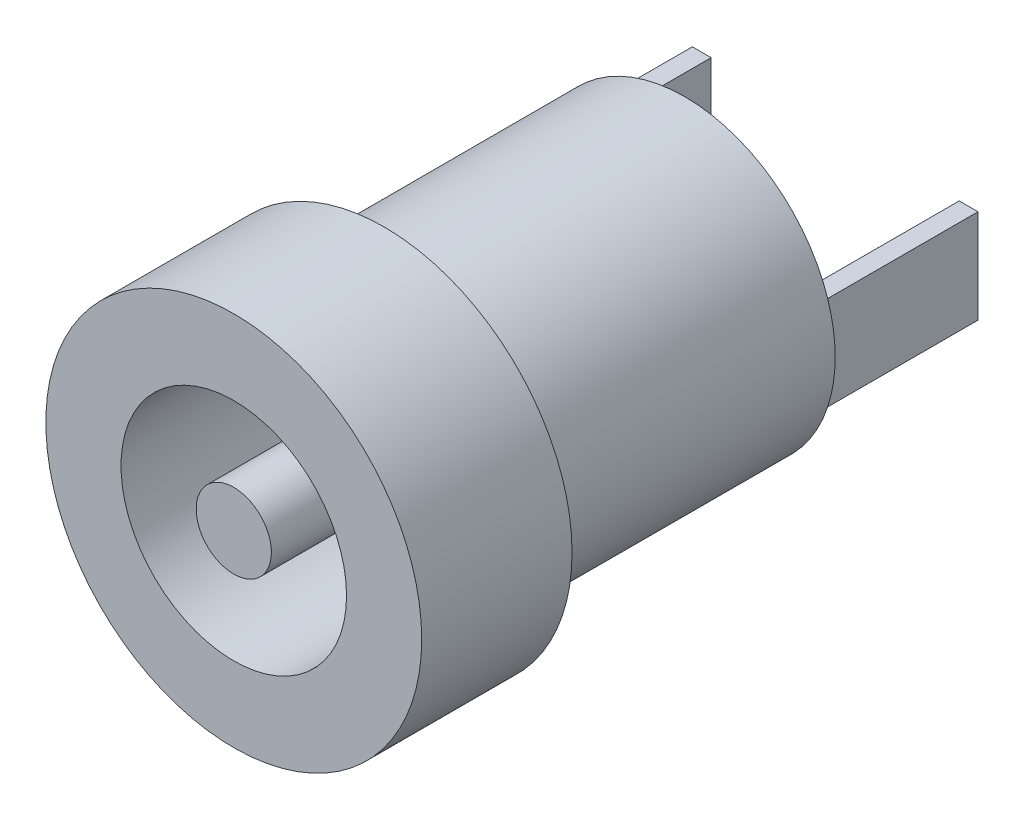
SolidWorks part; units mm, degrees
ref_plane "Front Plane" through (0, 0, 0) normal (0, 0, 1) x (1, 0, 0)
ref_plane "Top Plane" through (0, 0, 0) normal (0, 1, 0) x (1, 0, 0)
ref_plane "Right Plane" through (0, 0, 0) normal (1, 0, 0) x (0, 0, -1)
sketch "Sketch1" plane through (0, 0, 0) normal (0, 0, 1) x (1, 0, 0)
  circle A0 centre (0, 0) radius 5
  circle A1 centre (0, 0) radius 1
  circle A2 centre (0, 0) radius 3
  dimension "D1" = 10
  dimension "D2" = 2
  dimension "D3" = 2
extrude "Boss-Extrude1" add sketch "Sketch1" against normal blind 4 contours A0 A2 | A1
sketch "Sketch2" plane through (0, 0, -4) normal (0, 0, -1) x (-1, 0, 0)
  circle A0 centre (0, 0) radius 4
  dimension "D1" = 8
extrude "Boss-Extrude2" add sketch "Sketch2" along normal blind 8
sketch "Sketch3" plane through (0, 0, -12) normal (0, 0, -1) x (-1, 0, 0)
  line L0 (0, 0) -> (0, 4) construction
  line L1 (-3.8, 1.249) -> (-3.3, 1.249)
  line L2 (-3.8, 0) -> (-4, 0)
  line L3 (-3.8, 1.249) -> (-3.8, -1.249)
  line L4 (-3.8, -1.249) -> (-3.3, -1.249)
  line L5 (-3.3, 1.249) -> (-3.3, -1.249)
  line L6 (3.8, -1.249) -> (3.3, -1.249)
  line L7 (3.3, 1.249) -> (3.3, -1.249)
  line L8 (3.8, 1.249) -> (3.3, 1.249)
  line L9 (3.8, 1.249) -> (3.8, -1.249)
  circle A1 centre (0, 0) radius 4
  circle A2 centre (0, 0) radius 4
  dimension "D2" = 0.2
  dimension "D3" = 0.5
  dimension "D1" = 0
extrude "Boss-Extrude3" add sketch "Sketch3" along normal blind 4 contours L5 L1 L3 L4 | L9 L8 L7 L6
